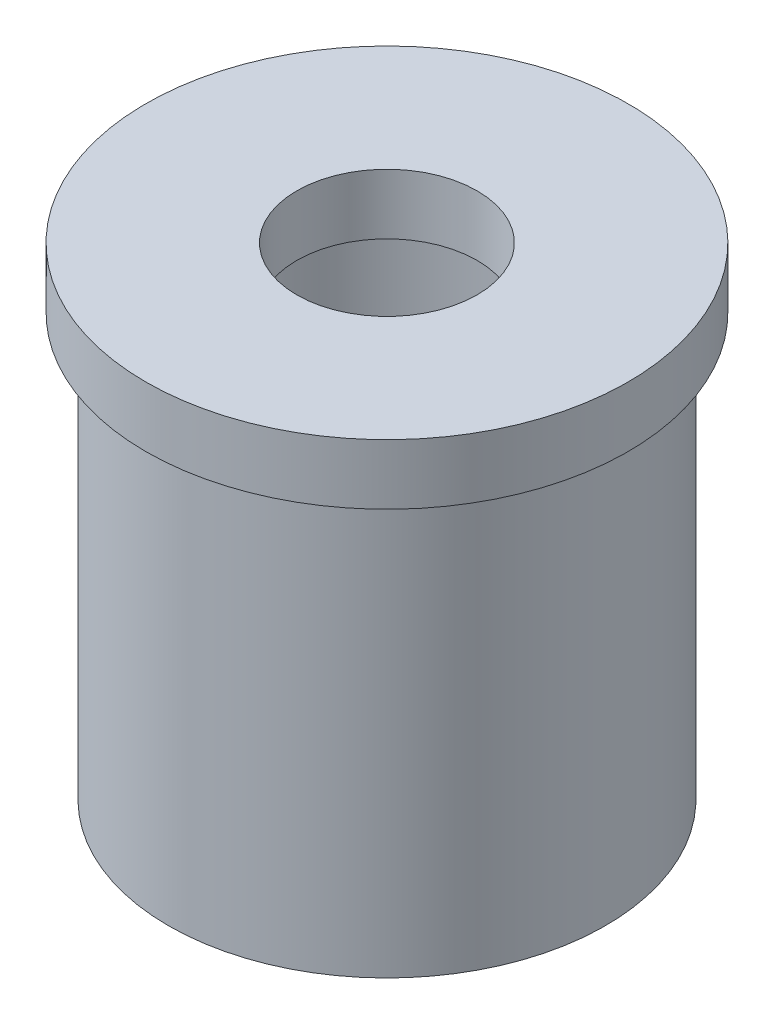
SolidWorks part; units mm, degrees
ref_plane "Front Plane" through (0, 0, 0) normal (0, 0, 1) x (1, 0, 0)
ref_plane "Top Plane" through (0, 0, 0) normal (0, 1, 0) x (1, 0, 0)
ref_plane "Right Plane" through (0, 0, 0) normal (1, 0, 0) x (0, 0, -1)
sketch "Sketch1" plane through (0, 0, 0) normal (0, 1, 0) x (1, 0, 0)
  circle A0 centre (0, 0) radius 23.0187
  dimension "D1" = 46.0375
extrude "Boss-Extrude1" add sketch "Sketch1" along normal blind 44.45
sketch "Sketch2" plane through (0, 44.45, 0) normal (0, 1, 0) x (1, 0, 0)
  circle A0 centre (0, 0) radius 25.4
  dimension "D1" = 50.8
extrude "Boss-Extrude2" add sketch "Sketch2" along normal blind 6.35
sketch "Sketch3" plane through (0, 50.8, 0) normal (0, 1, 0) x (1, 0, 0)
  circle A0 centre (0, 0) radius 9.5
  dimension "D1" = 19
extrude "Cut-Extrude1" cut sketch "Sketch3" against normal through all
sketch "Sketch4" plane through (0, 0, 0) normal (0, -1, 0) x (1, 0, 0)
  circle A0 centre (0, 0) radius 16.6751
  dimension "D1" = 33.3502
extrude "Cut-Extrude2" cut sketch "Sketch4" against normal blind 44.45
sketch "Sketch5" plane through (0, 0, 0) normal (0, -1, 0) x (1, 0, 0)
  circle A0 centre (0, 0) radius 19.8438 construction
  circle A1 centre (19.8438, 0) radius 1.5875
  circle A2 centre (9.9219, -17.1852) radius 1.5875
  circle A3 centre (-9.9219, -17.1852) radius 1.5875
  circle A4 centre (-19.8438, 0) radius 1.5875
  circle A5 centre (-9.9219, 17.1852) radius 1.5875
  circle A6 centre (9.9219, 17.1852) radius 1.5875
  point P17 (0, 0)
  dimension "D1" = 39.6875
  dimension "D2" = 3.175
  dimension "D3" = 6
extrude "Cut-Extrude3" cut sketch "Sketch5" against normal blind 19.05
ref_plane "Plane1" through (-23.0187, 0, 0) normal (-1, 0, 0) x (0, 0, 1)
hole_wizard "Tap Drill for 1/4-20 Tap1" positions "Sketch7" profile "Sketch9" hole size "1/4-20" standard "ANSI Inch"
sketch "Sketch7" plane through (-23.0187, 0, 0) normal (-1, 0, 0) x (0, 0, 1)
  line L0 (-23.0187, 44.45) -> (23.0187, 44.45) construction
  line L1 (0, 0) -> (0, 31.75) construction
  point P0 (0, 31.75)
  dimension "D1" = 12.7
sketch "Sketch9" plane through (-23.0187, 31.75, 0) normal (0, 1, 0) x (0, 0, 1)
  line L0 (0, 0) -> (0, 6.3436)
  line L1 (0, 6.3436) -> (2.5527, 6.3436)
  line L2 (2.5527, 6.3436) -> (2.5527, 0)
  line L5 (2.5527, 0) -> (0, 0)
  line L11 (0, -6.35) -> (0, 107.95) construction
  dimension "Thru Hole Dia." = 5.1054
  dimension "Thru Hole Depth" = 6.3436
